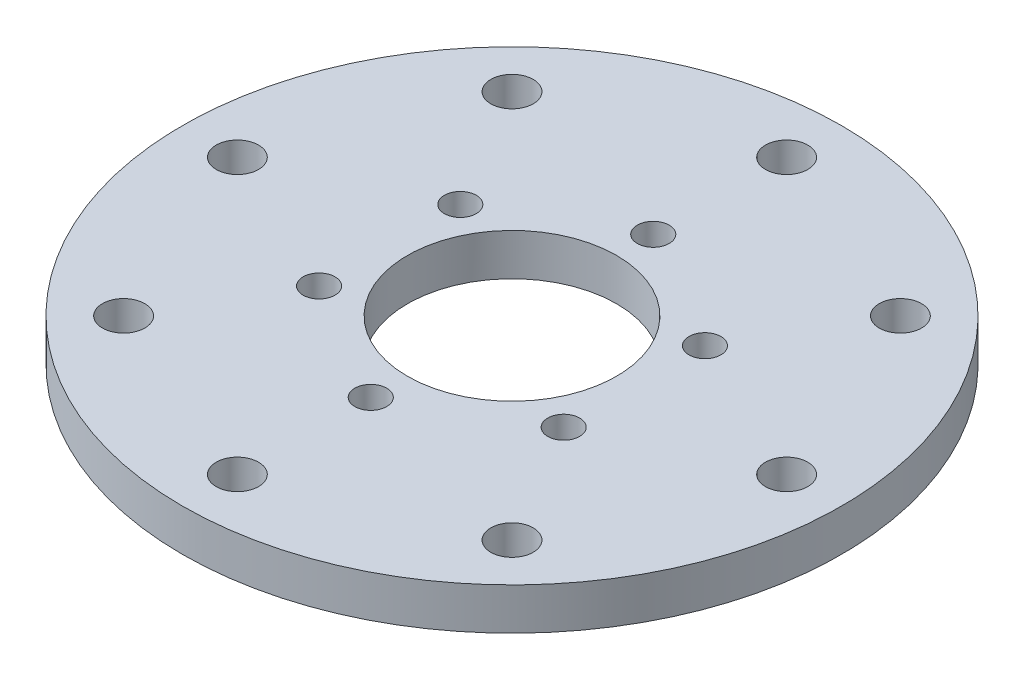
SolidWorks part; units mm, degrees
ref_plane "前视基准面" through (0, 0, 0) normal (0, 0, 1) x (1, 0, 0)
ref_plane "上视基准面" through (0, 0, 0) normal (0, 1, 0) x (1, 0, 0)
ref_plane "右视基准面" through (0, 0, 0) normal (1, 0, 0) x (0, 0, -1)
other "Configuration Table"
sketch "草图1" plane through (0, 0, 0) normal (0, 1, 0) x (1, 0, 0)
  circle A0 centre (0, 0) radius 31.5
  circle A1 centre (0, 0) radius 22.5
  dimension "D1" = 45
  dimension "D2" = 63
extrude "凸台-拉伸1" add sketch "草图1" along normal blind 4
sketch "草图2" plane through (0, 4, 0) normal (0, 1, 0) x (1, 0, 0)
  circle A0 centre (0, 0) radius 26.25 construction
  circle A1 centre (0, 26.25) radius 2.025
  circle A2 centre (18.5616, 18.5616) radius 2.025
  circle A3 centre (26.25, 0) radius 2.025
  circle A4 centre (18.5616, -18.5616) radius 2.025
  circle A5 centre (0, -26.25) radius 2.025
  circle A6 centre (-18.5616, -18.5616) radius 2.025
  circle A7 centre (-26.25, 0) radius 2.025
  circle A8 centre (-18.5616, 18.5616) radius 2.025
  point P21 (0, 0)
  dimension "D1" = 52.5
  dimension "D2" = 4.05
  dimension "D3" = 8
extrude "切除-拉伸1" cut sketch "草图2" against normal through all both and the other way through all
sketch "草图3" plane through (0, 4, 0) normal (0, 1, 0) x (1, 0, 0)
  circle A0 centre (0, 0) radius 22.5
  dimension "D1" = 45
extrude "凸台-拉伸2" add sketch "草图3" against normal up to surface (4 mm away) up to face at (0, 0, -24.225)
sketch "草图4" plane through (0, 0, 0) normal (0, -1, 0) x (1, 0, 0)
  circle A0 centre (0, 0) radius 13.5 construction
  circle A1 centre (0, 13.5) radius 1.525
  circle A2 centre (11.6913, 6.75) radius 1.525
  circle A3 centre (11.6913, -6.75) radius 1.525
  circle A4 centre (0, -13.5) radius 1.525
  circle A5 centre (-11.6913, -6.75) radius 1.525
  circle A6 centre (-11.6913, 6.75) radius 1.525
  point P18 (0, 0)
  dimension "D1" = 27
  dimension "D2" = 3.05
  dimension "D3" = 6
extrude "切除-拉伸2" cut sketch "草图4" against normal up to surface (4 mm away) up to face at (0, 4, -24.225)
sketch "草图5" plane through (0, 0, 0) normal (0, -1, 0) x (1, 0, 0)
  circle A0 centre (0, 0) radius 10
  dimension "D1" = 20
extrude "切除-拉伸3" cut sketch "草图5" against normal up to surface (4 mm away) up to face at (0, 4, 15.025)
